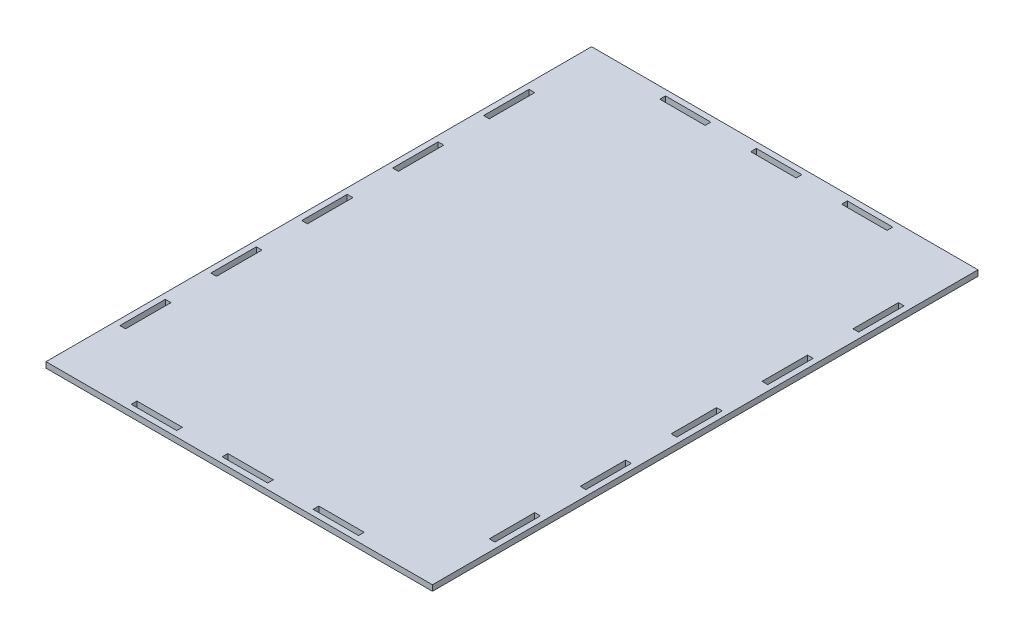
SolidWorks part; units mm, degrees
ref_plane "Front Plane" through (0, 0, 0) normal (0, 0, 1) x (1, 0, 0)
ref_plane "Top Plane" through (0, 0, 0) normal (0, 1, 0) x (1, 0, 0)
ref_plane "Right Plane" through (0, 0, 0) normal (1, 0, 0) x (0, 0, -1)
sketch "Sketch1" plane through (0, 0, 0) normal (0, 1, 0) x (1, 0, 0)
  line L0 (-104.775, -149.225) -> (104.775, -149.225) construction
  line L1 (-107.95, -152.4) -> (107.95, -152.4)
  line L2 (-107.95, -152.4) -> (-107.95, 152.4)
  line L3 (-107.95, 152.4) -> (107.95, 152.4)
  line L4 (107.95, -152.4) -> (107.95, 152.4)
  line L5 (-107.95, -152.4) -> (107.95, 152.4) construction
  line L6 (-107.95, 152.4) -> (107.95, -152.4) construction
  line L7 (104.775, -149.225) -> (104.775, 149.225) construction
  line L8 (104.775, 149.225) -> (-104.775, 149.225) construction
  line L9 (-104.775, 149.225) -> (-104.775, -149.225) construction
  line L10 (-104.775, 149.225) -> (-104.775, 152.4) construction
  line L11 (-104.775, 149.225) -> (-107.95, 149.225) construction
  line L12 (104.775, -149.225) -> (104.775, -152.4) construction
  line L13 (104.775, -149.225) -> (107.95, -149.225) construction
  line L14 (-101.6, 149.225) -> (-101.6, 146.05) construction
  line L15 (-101.6, -146.05) -> (101.6, -146.05) construction
  line L16 (-101.6, -146.05) -> (-101.6, 146.05) construction
  line L17 (-101.6, 146.05) -> (101.6, 146.05) construction
  line L18 (101.6, -146.05) -> (101.6, 146.05) construction
  line L19 (-101.6, -146.05) -> (101.6, 146.05) construction
  line L20 (-101.6, 146.05) -> (101.6, -146.05) construction
  line L21 (-101.6, 146.05) -> (-104.775, 146.05) construction
  line L22 (101.6, -149.225) -> (101.6, -146.05) construction
  line L23 (101.6, -146.05) -> (104.775, -146.05) construction
  line L24 (104.775, 12.7) -> (104.775, 38.1) construction
  line L25 (-12.7, 146.05) -> (12.7, 146.05)
  line L26 (-12.7, 146.05) -> (-12.7, 149.225)
  line L27 (-12.7, 149.225) -> (12.7, 149.225)
  line L28 (12.7, 146.05) -> (12.7, 149.225)
  line L29 (38.1, 146.05) -> (63.5, 146.05)
  line L30 (38.1, 146.05) -> (38.1, 149.225)
  line L31 (38.1, 149.225) -> (63.5, 149.225)
  line L32 (63.5, 146.05) -> (63.5, 149.225)
  line L33 (-63.5, 146.05) -> (-38.1, 146.05)
  line L34 (-63.5, 146.05) -> (-63.5, 149.225)
  line L35 (-63.5, 149.225) -> (-38.1, 149.225)
  line L36 (-38.1, 146.05) -> (-38.1, 149.225)
  line L37 (-63.5, -146.05) -> (-38.1, -146.05)
  line L38 (-63.5, -146.05) -> (-63.5, -149.225)
  line L39 (-63.5, -149.225) -> (-38.1, -149.225)
  line L40 (-38.1, -146.05) -> (-38.1, -149.225)
  line L41 (-12.7, -146.05) -> (12.7, -146.05)
  line L42 (-12.7, -146.05) -> (-12.7, -149.225)
  line L43 (-12.7, -149.225) -> (12.7, -149.225)
  line L44 (12.7, -146.05) -> (12.7, -149.225)
  line L45 (38.1, -146.05) -> (63.5, -146.05)
  line L46 (38.1, -146.05) -> (38.1, -149.225)
  line L47 (38.1, -149.225) -> (63.5, -149.225)
  line L48 (63.5, -146.05) -> (63.5, -149.225)
  line L49 (101.6, -12.7) -> (104.775, -12.7)
  line L50 (101.6, -12.7) -> (101.6, 12.7)
  line L51 (101.6, 12.7) -> (104.775, 12.7)
  line L52 (104.775, -12.7) -> (104.775, 12.7)
  line L53 (101.6, 38.1) -> (104.775, 38.1)
  line L54 (101.6, 38.1) -> (101.6, 63.5)
  line L55 (101.6, 63.5) -> (104.775, 63.5)
  line L56 (104.775, 38.1) -> (104.775, 63.5)
  line L57 (101.6, 88.9) -> (104.775, 88.9)
  line L58 (101.6, 88.9) -> (101.6, 114.3)
  line L59 (101.6, 114.3) -> (104.775, 114.3)
  line L60 (104.775, 88.9) -> (104.775, 114.3)
  line L61 (101.6, -38.1) -> (104.775, -38.1)
  line L62 (101.6, -38.1) -> (101.6, -63.5)
  line L63 (101.6, -63.5) -> (104.775, -63.5)
  line L64 (104.775, -38.1) -> (104.775, -63.5)
  line L65 (101.6, -88.9) -> (104.775, -88.9)
  line L66 (101.6, -88.9) -> (101.6, -114.3)
  line L67 (101.6, -114.3) -> (104.775, -114.3)
  line L68 (104.775, -88.9) -> (104.775, -114.3)
  line L69 (104.775, 63.5) -> (104.775, 88.9) construction
  line L70 (104.775, -38.1) -> (104.775, -12.7)
  line L71 (104.775, -63.5) -> (104.775, -88.9)
  line L73 (-101.6, 114.3) -> (-104.775, 114.3)
  line L74 (-101.6, 114.3) -> (-101.6, 88.9)
  line L75 (-101.6, 88.9) -> (-104.775, 88.9)
  line L76 (-104.775, 114.3) -> (-104.775, 88.9)
  line L77 (-101.6, 63.5) -> (-104.775, 63.5)
  line L78 (-101.6, 63.5) -> (-101.6, 38.1)
  line L79 (-101.6, 38.1) -> (-104.775, 38.1)
  line L80 (-104.775, 63.5) -> (-104.775, 38.1)
  line L81 (-101.6, 12.7) -> (-104.775, 12.7)
  line L82 (-101.6, 12.7) -> (-101.6, -12.7)
  line L83 (-101.6, -12.7) -> (-104.775, -12.7)
  line L84 (-104.775, 12.7) -> (-104.775, -12.7)
  line L85 (-101.6, -38.1) -> (-104.775, -38.1)
  line L86 (-101.6, -38.1) -> (-101.6, -63.5)
  line L87 (-101.6, -63.5) -> (-104.775, -63.5)
  line L88 (-104.775, -38.1) -> (-104.775, -63.5)
  line L89 (-101.6, -88.9) -> (-104.775, -88.9)
  line L90 (-101.6, -88.9) -> (-101.6, -114.3)
  line L91 (-101.6, -114.3) -> (-104.775, -114.3)
  line L92 (-104.775, -88.9) -> (-104.775, -114.3)
  point P0 (0, 0)
  point P9 (0, 0)
  point P35 (0, 149.225)
  point P68 (101.6, 0)
  point P89 (0, 0)
  point P90 (0, 0)
  point P91 (0, 0)
  point P92 (0, 0)
  dimension "D1" = 304.8
  dimension "D2" = 215.9
  dimension "D3" = 3.175
  dimension "D4" = 25.4
  dimension "D5" = 25.4
  dimension "D6" = 25.4
  dimension "D7" = 25.4
extrude "Boss-Extrude1" add sketch "Sketch1" along normal mid plane 3.175 contours L1 L4 L3 L2 L92 L89 L90 L91 L88 L85 L86 L87 L84 L81 L82 L83 L80 L77 L78 L79 L76 L73 L74 L75 L60 L57 L58 L59 L56 L53 L54 L55 L36 L33 L34 L35 L32 L29 L30 L31 L28
